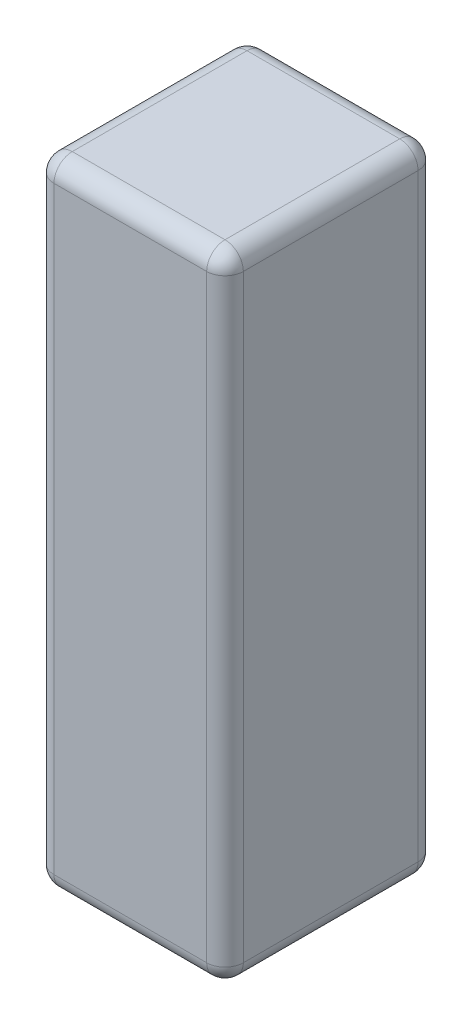
SolidWorks part; units mm, degrees
material "Lipo 3S"
ref_plane "Front Plane" through (0, 0, 0) normal (0, 0, 1) x (1, 0, 0)
ref_plane "Top Plane" through (0, 0, 0) normal (0, 1, 0) x (1, 0, 0)
ref_plane "Right Plane" through (0, 0, 0) normal (1, 0, 0) x (0, 0, -1)
sketch "Sketch1" plane through (0, 0, 0) normal (0, 1, 0) x (1, 0, 0)
  line L1 (0, 0) -> (31, 0)
  line L2 (0, 0) -> (0, 34.6)
  line L3 (0, 34.6) -> (31, 34.6)
  line L4 (31, 0) -> (31, 34.6)
  dimension "D1" = 34.6
  dimension "D2" = 31
extrude "Boss-Extrude1" add sketch "Sketch1" along normal blind 104
fillet "Fillet1" radius 3 12 edges at (15.5, 104, -34.6) (15.5, 0, -34.6) (0, 52, -34.6) (0, 104, -17.3) (0, 0, -17.3) (31, 104, -17.3) (31, 52, -34.6) (31, 0, -17.3) (0, 52, 0) (15.5, 104, 0) (31, 52, 0) (15.5, 0, 0)
